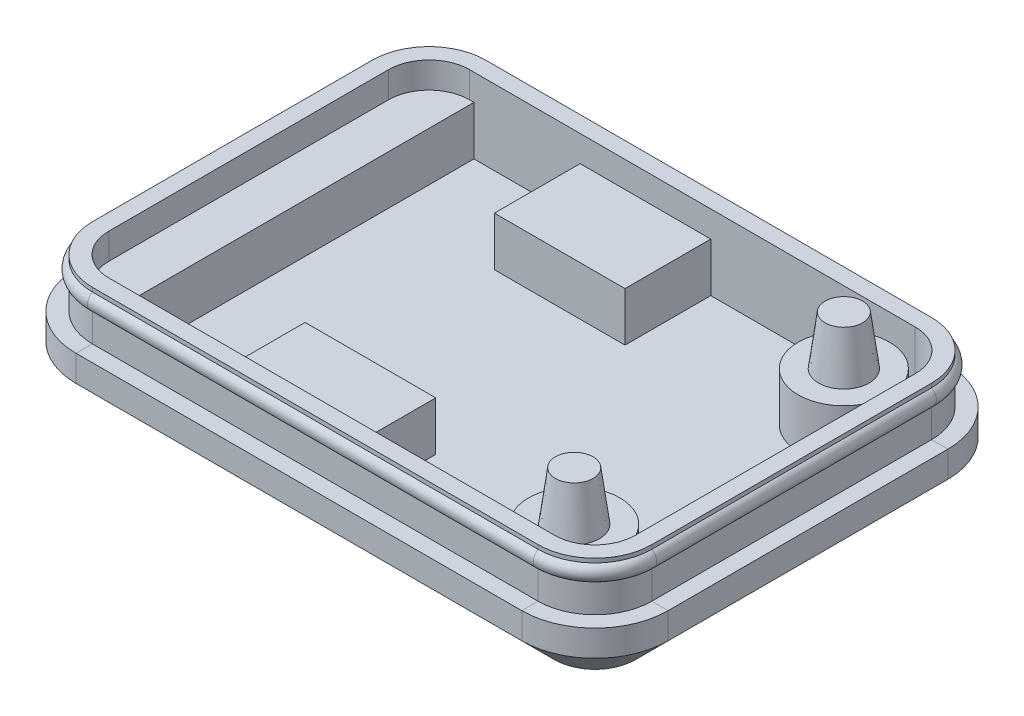
SolidWorks part; units mm, degrees
ref_plane "Front Plane" through (0, 0, 0) normal (0, 0, 1) x (1, 0, 0)
ref_plane "Top Plane" through (0, 0, 0) normal (0, 1, 0) x (1, 0, 0)
ref_plane "Right Plane" through (0, 0, 0) normal (1, 0, 0) x (0, 0, -1)
sketch "pcb-outline" plane through (0, 0, 0) normal (0, 1, 0) x (1, 0, 0)
  line L0 (27.94, 19.05) -> (27.94, 2.54) construction
  line L1 (2.23, 0) -> (29.52, 0)
  line L2 (0, 2.23) -> (0, 19.36)
  line L3 (2.23, 21.59) -> (29.52, 21.59)
  line L4 (31.75, 2.23) -> (31.75, 19.36)
  arc A0 (2.23, 0) -> (0, 2.23) centre (2.23, 2.23) cw
  arc A1 (29.52, 0) -> (31.75, 2.23) centre (29.52, 2.23) ccw
  arc A2 (29.52, 21.59) -> (31.75, 19.36) centre (29.52, 19.36) cw
  arc A3 (0, 19.36) -> (2.23, 21.59) centre (2.23, 19.36) cw
  circle A4 centre (27.94, 19.05) radius 1.795
  circle A5 centre (27.94, 2.54) radius 1.795
  point P7 (0, 0)
  point P10 (31.75, 0)
  point P15 (0, 21.59)
  point P20 (0, 10.795)
  point P21 (27.94, 10.795)
  point P22 (0, 0)
  dimension "D3" = 2.23
  dimension "D6" = 3.59
  dimension "D1" = 21.59
  dimension "D2" = 31.75
  dimension "D4" = 16.51
  dimension "D5" = 27.94
sketch "Sketch2" plane through (0, 0, 0) normal (0, 1, 0) x (1, 0, 0)
  line L0 (-0.25, 19.36) -> (-0.25, 2.23)
  line L1 (2.23, -0.25) -> (29.52, -0.25)
  line L2 (32, 2.23) -> (32, 19.36)
  line L3 (29.52, 21.84) -> (2.23, 21.84)
  line L4 (31.75, 2.23) -> (31.75, 19.36) construction
  arc A0 (-0.25, 2.23) -> (2.23, -0.25) centre (2.23, 2.23) ccw
  arc A1 (29.52, -0.25) -> (32, 2.23) centre (29.52, 2.23) ccw
  arc A2 (32, 19.36) -> (29.52, 21.84) centre (29.52, 19.36) ccw
  arc A3 (2.23, 21.84) -> (-0.25, 19.36) centre (2.23, 19.36) ccw
  point P12 (0, 0)
  point P15 (29.52, 2.23)
  point P17 (29.52, 23.8204)
  dimension "D1" = 0.25
extrude "main-extrusion" add sketch "Sketch2" along normal blind 1.6 and the other way blind 3 thin
sketch "Sketch3" plane through (0, -3, 0) normal (0, -1, 0) x (1, 0, 0)
  line L0 (-2.25, -19.36) -> (-2.25, -2.23)
  line L1 (2.23, 2.25) -> (29.52, 2.25)
  line L2 (34, -2.23) -> (34, -19.36)
  line L3 (29.52, -23.84) -> (2.23, -23.84)
  arc A0 (-2.25, -2.23) -> (2.23, 2.25) centre (2.23, -2.23) cw
  arc A1 (29.52, 2.25) -> (34, -2.23) centre (29.52, -2.23) cw
  arc A2 (34, -19.36) -> (29.52, -23.84) centre (29.52, -19.36) cw
  arc A3 (2.23, -23.84) -> (-2.25, -19.36) centre (2.23, -19.36) cw
extrude "tapered-bottom" add sketch "Sketch3" along normal blind 2 draft 45
sketch "Sketch4" plane through (0, 0, 0) normal (0, 1, 0) x (1, 0, 0)
  line L0 (29.52, 21.84) -> (2.23, 21.84) construction
  line L1 (2.5, 21.84) -> (-0.25, 21.84)
  line L2 (2.5, 21.84) -> (2.5, -0.25)
  line L3 (2.5, -0.25) -> (-0.25, -0.25)
  line L4 (-0.25, 21.84) -> (-0.25, -0.25)
  line L5 (2.23, -0.25) -> (29.52, -0.25) construction
  line L6 (-0.25, 19.36) -> (-0.25, 2.23) construction
  line L7 (0, 2.23) -> (0, 19.36) construction
  line L8 (2.23, -0.25) -> (29.52, -0.25) construction
  line L9 (17, 21.84) -> (9, 21.84)
  line L10 (17, 21.84) -> (17, 16.59)
  line L11 (17, 16.59) -> (9, 16.59)
  line L12 (9, 21.84) -> (9, 16.59)
  line L13 (9, -0.25) -> (17, -0.25)
  line L14 (9, -0.25) -> (9, 5)
  line L15 (9, 5) -> (17, 5)
  line L16 (17, -0.25) -> (17, 5)
  line L17 (2.23, 21.59) -> (29.52, 21.59) construction
  circle A0 centre (27.94, 19.05) radius 2.795
  circle A1 centre (27.94, 2.54) radius 2.795
  circle A3 centre (27.94, 19.05) radius 1.795 construction
  point P30 (6.3224, 5.9063)
  dimension "D1" = 1
  dimension "D2" = 2.5
  dimension "D3" = 5
  dimension "D4" = 9
  dimension "D5" = 17
sketch "Sketch5" plane through (0, 0, 0) normal (0, 1, 0) x (1, 0, 0)
  circle A0 centre (27.94, 19.05) radius 1.545
  circle A1 centre (27.94, 2.54) radius 1.545
  circle A2 centre (27.94, 19.05) radius 1.795 construction
  dimension "D1" = 0.25
extrude "PCB-support" add sketch "Sketch4" against normal up to next
extrude "guide-pins" add sketch "Sketch5" along normal blind 3 draft 7.5
sketch "path" plane through (0, 1.6, 0) normal (0, 1, 0) x (1, 0, 0)
  line L0 (2.23, -0.25) -> (29.52, -0.25)
  line L1 (32, 2.23) -> (32, 19.36)
  line L2 (29.52, 21.84) -> (2.23, 21.84)
  line L3 (-0.25, 19.36) -> (-0.25, 2.23) construction
  line L4 (-0.25, 19.36) -> (-0.25, 2.23)
  arc A0 (29.52, -0.25) -> (32, 2.23) centre (29.52, 2.23) ccw
  arc A1 (32, 19.36) -> (29.52, 21.84) centre (29.52, 19.36) ccw
  arc A2 (2.23, 21.84) -> (-0.25, 19.36) centre (2.23, 19.36) ccw
  arc A3 (-0.25, 2.23) -> (2.23, -0.25) centre (2.23, 2.23) ccw
ref_plane "Plane1" through (2.23, 0, 0) normal (1, 0, 0) x (0, 0, -1)
sketch "profile" plane through (2.23, 0, 0) normal (1, 0, 0) x (0, 0, -1)
  line L0 (-2.25, 1.6) -> (-2.25, -1.4)
  line L1 (-2.25, -3) -> (-2.25, 1.6) construction
  line L2 (-2.25, -1.4) -> (-1.25, -1.4)
  line L3 (-1.25, -1.4) -> (-1.25, 0.35)
  line L4 (-1.25, 1.35) -> (-1.25, 1.6)
  line L5 (-1.25, 1.6) -> (-2.25, 1.6)
  line L6 (2.23, 1.6) -> (-2.25, 1.6) construction
  arc A0 (-1.25, 0.35) -> (-1.25, 1.35) centre (-0.9833, 0.85) cw
  point P9 (-1.55, 0.85)
  point P10 (-1.1, 0.9677)
  point P11 (-1.1, -0.2751)
  point P14 (-0.9835, 0.7551)
  dimension "D1" = 3
  dimension "D2" = 1
  dimension "D3" = 0.3
  dimension "D4" = 1
  dimension "D5" = 0.75
sweep "top-ridge" cut profiles "profile" path "path"
